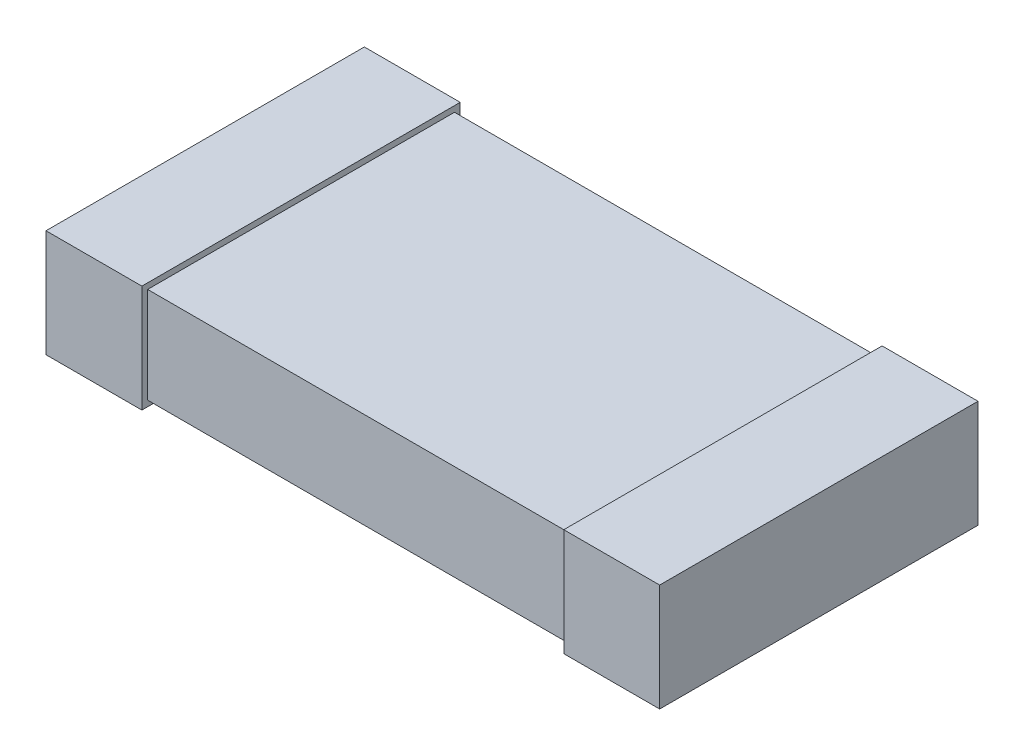
SolidWorks part; units mm, degrees
ref_plane "Front Plane" through (0, 0, 0) normal (0, 0, 1) x (1, 0, 0)
ref_plane "Top Plane" through (0, 0, 0) normal (0, 1, 0) x (1, 0, 0)
ref_plane "Right Plane" through (0, 0, 0) normal (1, 0, 0) x (0, 0, -1)
sketch "Sketch1" plane through (0, 0, 0) normal (0, 1, 0) x (1, 0, 0)
  line L1 (-1.6, 0.8) -> (1.6, 0.8)
  line L2 (-1.6, 0.8) -> (-1.6, -0.8)
  line L3 (-1.6, -0.8) -> (1.6, -0.8)
  line L4 (1.6, 0.8) -> (1.6, -0.8)
  point P4 (0, 0.8)
  point P6 (1.6, 0)
  dimension "D1" = 1.6
  dimension "D2" = 3.2
extrude "Extrude1" add sketch "Sketch1" along normal blind 0.5
sketch "Sketch2" plane through (0, 0, 0) normal (0, 0, 1) x (1, 0, 0)
  line L0 (-1.6, 0.5) -> (-1.6, 0) construction
  line L1 (-1.1, 0.53) -> (-1.6, 0.53)
  line L2 (-1.1, 0.53) -> (-1.1, -0.03)
  line L3 (-1.1, -0.03) -> (-1.6, -0.03)
  line L4 (-1.6, 0.53) -> (-1.6, -0.03)
  line L5 (-1.6, 0.5) -> (1.6, 0.5) construction
  line L6 (-1.6, 0) -> (1.6, 0) construction
  line L7 (0, 0) -> (0, -0.3575) construction
  line L8 (1.6, 0.53) -> (1.6, -0.03)
  line L9 (1.1, -0.03) -> (1.6, -0.03)
  line L10 (1.1, 0.53) -> (1.1, -0.03)
  line L11 (1.1, 0.53) -> (1.6, 0.53)
  dimension "D1" = 0.5
  dimension "D2" = 0.03
  dimension "D3" = 0.03
extrude "Extrude2" add sketch "Sketch2" along normal offset from surface 0.03 and the other way offset from surface (0.83 mm away) 0.03 up to face at (0, 0.25, 0.8) offset beyond the face yes other way up to face at (0, 0.25, -0.8)
ref_plane "Board Surface" through (0, -0.03, 0) normal (0, 1, 0) x (-1, 0, 0)
sketch "Component_Outline" plane through (0, -0.03, 0) normal (0, 1, 0) x (-1, 0, 0)
  line L0 (1.6, 0.83) -> (1.1, 0.83)
  line L1 (1.1, 0.83) -> (1.1, 0.8)
  line L2 (1.1, 0.8) -> (-1.1, 0.8)
  line L3 (-1.1, 0.8) -> (-1.1, 0.83)
  line L4 (-1.1, 0.83) -> (-1.6, 0.83)
  line L5 (-1.6, 0.83) -> (-1.6, -0.83)
  line L6 (-1.6, -0.83) -> (-1.1, -0.83)
  line L7 (-1.1, -0.83) -> (-1.1, -0.8)
  line L8 (-1.1, -0.8) -> (1.1, -0.8)
  line L9 (1.1, 0.83) -> (1.1, -0.83) construction
  line L10 (1.1, -0.8) -> (1.1, 0.8) construction
  line L11 (1.1, -0.8) -> (1.1, -0.83)
  line L12 (1.1, -0.83) -> (1.6, -0.83)
  line L13 (1.6, -0.83) -> (1.6, 0.83)
  point P4 (0, 0)
